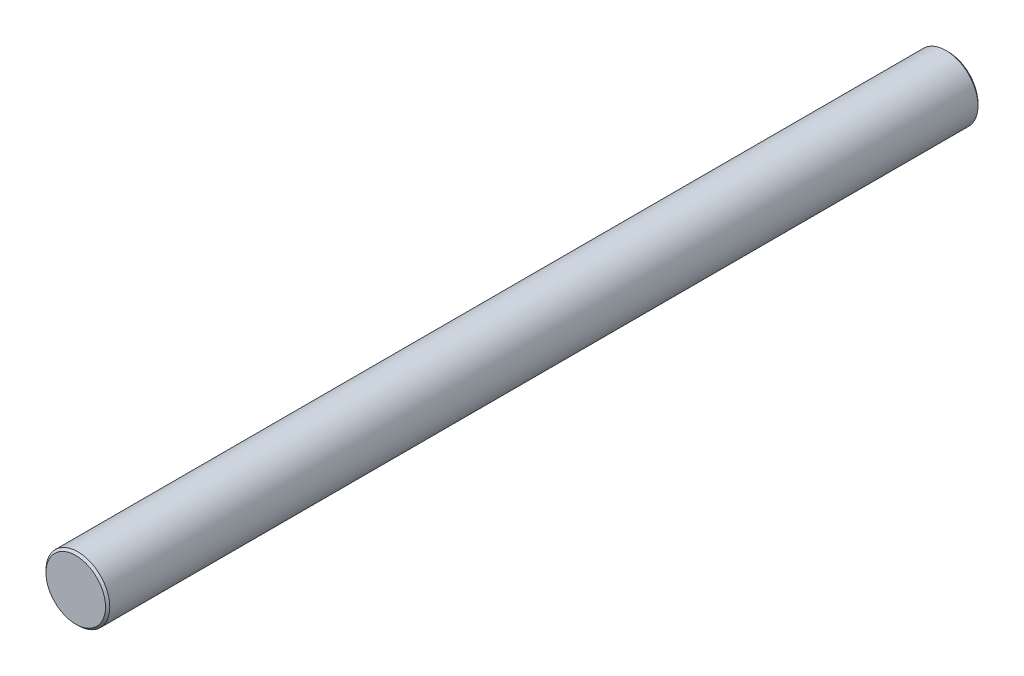
SolidWorks part; units mm, degrees
ref_plane "Front Plane" through (0, 0, 0) normal (0, 0, 1) x (1, 0, 0)
ref_plane "Top Plane" through (0, 0, 0) normal (0, 1, 0) x (1, 0, 0)
ref_plane "Right Plane" through (0, 0, 0) normal (1, 0, 0) x (0, 0, -1)
sketch "Sketch1" plane through (0, 0, 0) normal (0, 0, 1) x (1, 0, 0)
  circle A0 centre (0, 0) radius 3
  dimension "D1" = 6
extrude "Boss-Extrude1" add sketch "Sketch1" along normal blind 82
chamfer "Chamfer1" distance 0.2 angle 45 2 edges at (3, 0, 0) (3, 0, 82)
